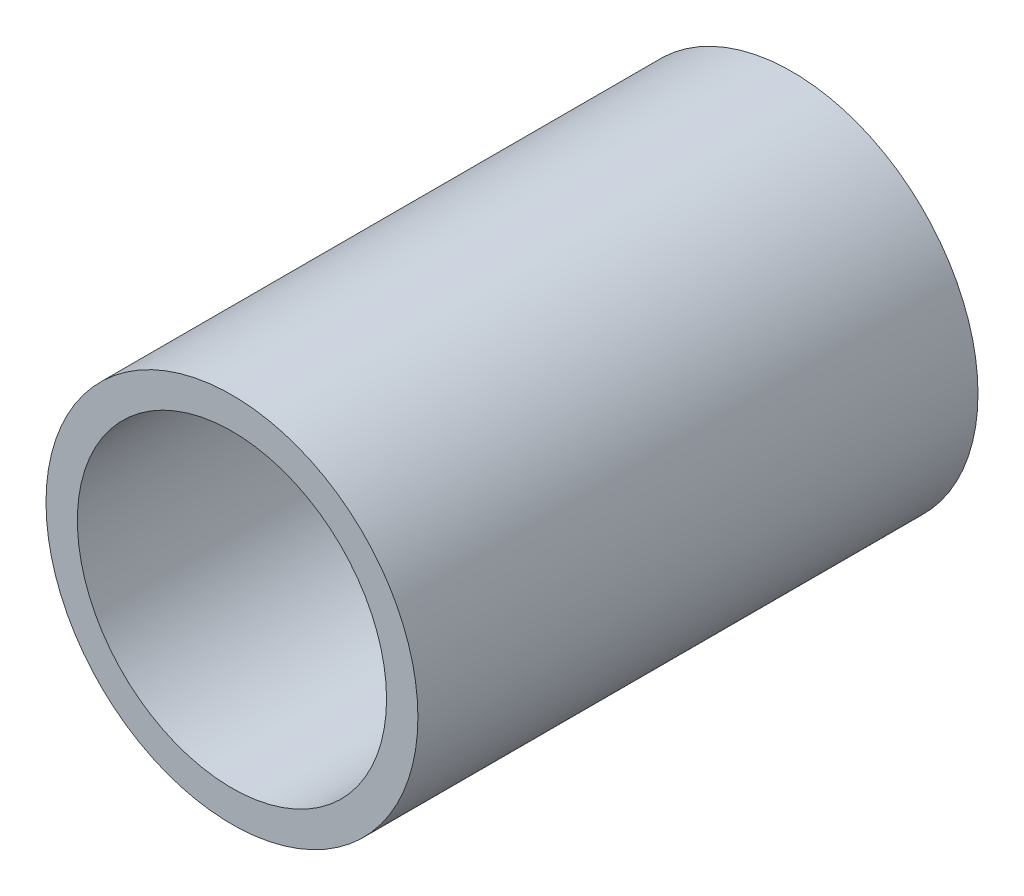
SolidWorks part; units mm, degrees
material "6061 Alloy"
ref_plane "Front Plane" through (0, 0, 0) normal (0, 0, 1) x (1, 0, 0)
ref_plane "Top Plane" through (0, 0, 0) normal (0, 1, 0) x (1, 0, 0)
ref_plane "Right Plane" through (0, 0, 0) normal (1, 0, 0) x (0, 0, -1)
sketch "Sketch1" plane through (0, 0, 0) normal (0, 0, 1) x (1, 0, 0)
  circle A0 centre (0, 0) radius 21.082
  circle A1 centre (0, 0) radius 17.526
  dimension "D3" = 42.164
  dimension "D1" = 35.052
extrude "Boss-Extrude1" add sketch "Sketch1" along normal blind 63.5
